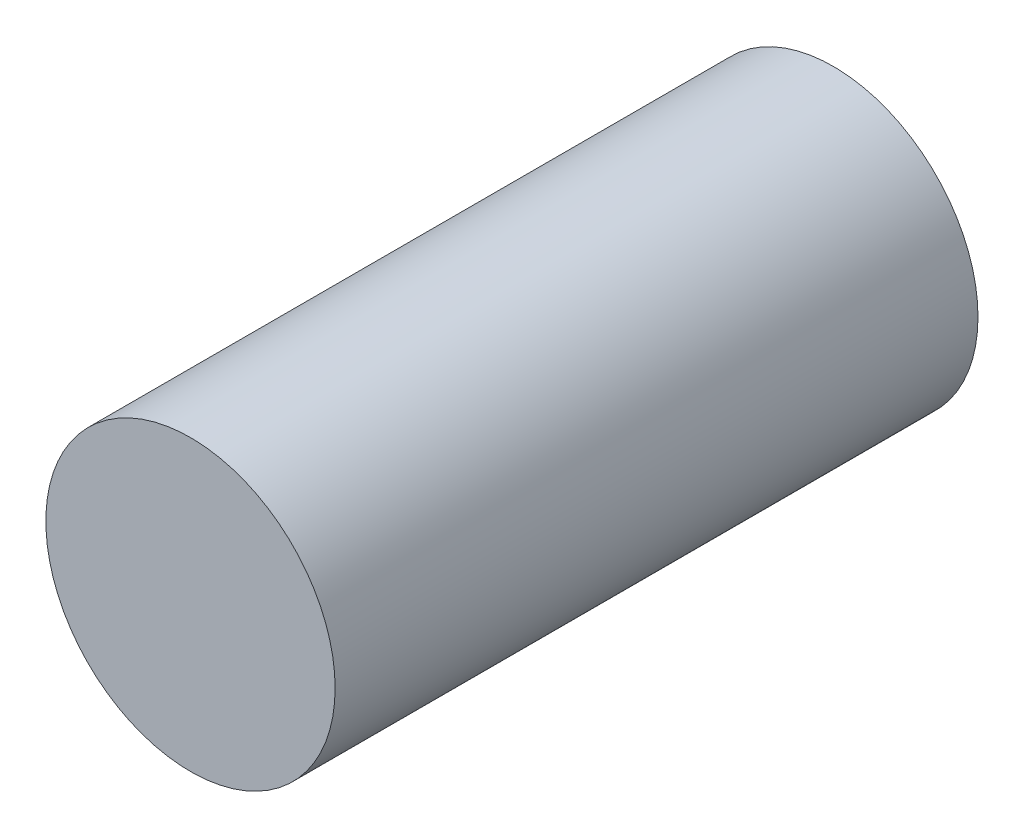
SolidWorks part; units mm, degrees
ref_plane "Front Plane" through (0, 0, 0) normal (0, 0, 1) x (1, 0, 0)
ref_plane "Top Plane" through (0, 0, 0) normal (0, 1, 0) x (1, 0, 0)
ref_plane "Right Plane" through (0, 0, 0) normal (1, 0, 0) x (0, 0, -1)
sketch "Sketch1" plane through (0, 0, 0) normal (0, 0, 1) x (1, 0, 0)
  circle A0 centre (0, 43.1384) radius 4.5
  dimension "D1" = 9
extrude "Boss-Extrude1" add sketch "Sketch1" along normal blind 14 and the other way blind 6 contours A0
